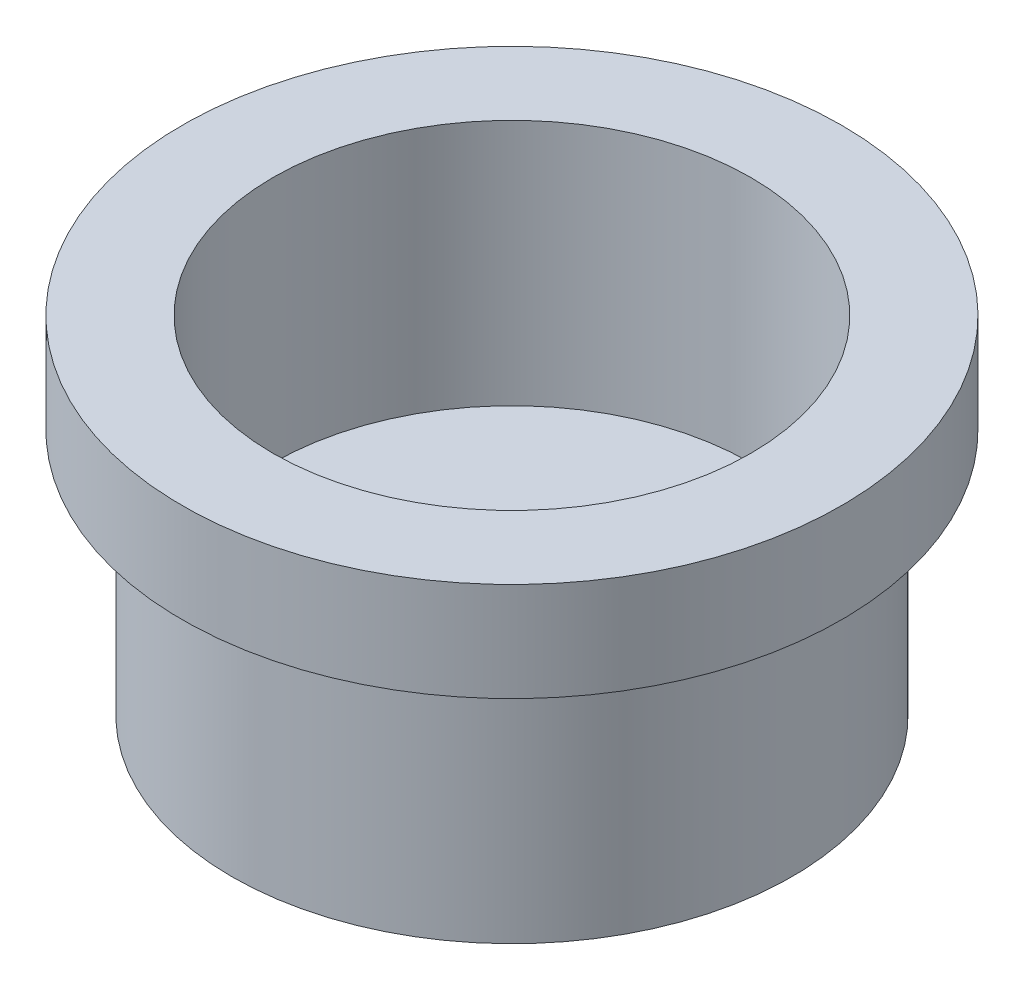
SolidWorks part; units mm, degrees
ref_plane "前视基准面" through (0, 0, 0) normal (0, 0, 1) x (1, 0, 0)
ref_plane "上视基准面" through (0, 0, 0) normal (0, 1, 0) x (1, 0, 0)
ref_plane "右视基准面" through (0, 0, 0) normal (1, 0, 0) x (0, 0, -1)
sketch "草图1" plane through (0, 0, 0) normal (0, 0, 1) x (1, 0, 0)
  line L0 (0, 0) -> (-5, 0) construction
  line L1 (-2.5, 0) -> (-2.5, 8)
  line L2 (-2.5, 8) -> (-4.7, 8)
  line L3 (-4.7, 8) -> (-4.7, 12)
  line L4 (-4.7, 12) -> (-14.5, 12)
  line L5 (-14.5, 12) -> (-14.5, 27)
  line L6 (-14.5, 27) -> (-20, 27)
  line L7 (-20, 27) -> (-20, 21)
  line L8 (-20, 21) -> (-17, 21)
  line L9 (-17, 21) -> (-17, 6)
  line L10 (-17, 6) -> (-6.5, 6)
  line L11 (-6.5, 6) -> (-6.5, 5)
  line L12 (-6.5, 5) -> (-4.5, 5)
  line L13 (-4.5, 5) -> (-4.5, 0)
  line L14 (-4.5, 0) -> (-2.5, 0)
  line L15 (0, 0) -> (0, 7.9072) construction
  point P12 (0, 3.9536)
  dimension "D1" = 2.5
  dimension "D2" = 4.5
  dimension "D3" = 2
  dimension "D4" = 6
  dimension "D5" = 1
  dimension "D6" = 3
  dimension "D7" = 4.7
  dimension "D8" = 4
  dimension "D9" = 15
  dimension "D10" = 6
  dimension "D11" = 20
  dimension "D12" = 17
  dimension "D13" = 14.5
revolve "旋转1" add sketch "草图1" angle 360 about L15
